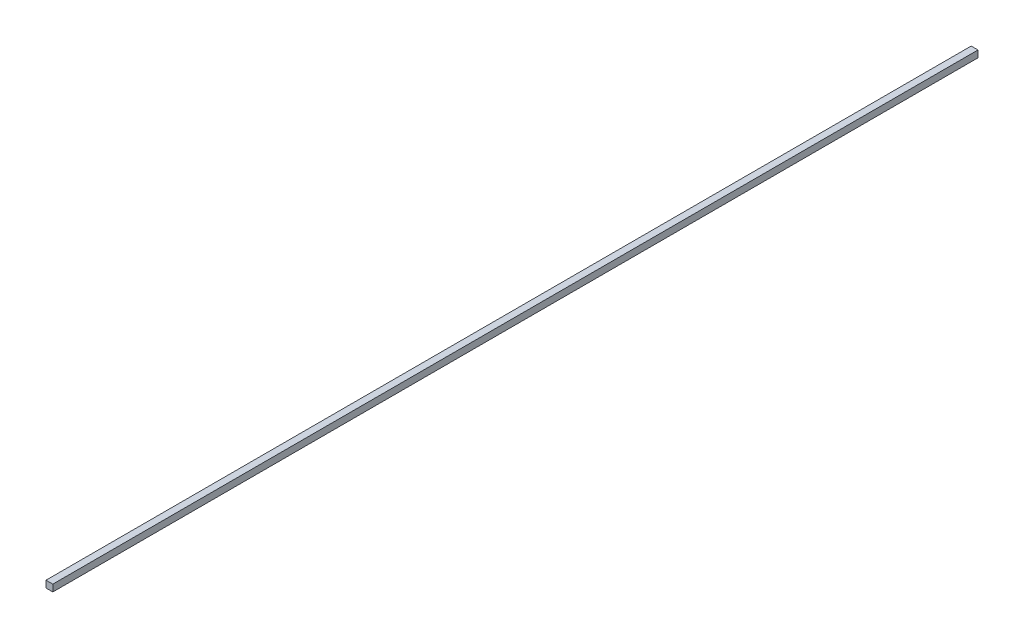
SolidWorks part; units mm, degrees
ref_plane "Plano frontal" through (0, 0, 0) normal (0, 0, 1) x (1, 0, 0)
ref_plane "Plano superior" through (0, 0, 0) normal (0, 1, 0) x (1, 0, 0)
ref_plane "Plano direito" through (0, 0, 0) normal (1, 0, 0) x (0, 0, -1)
sketch "Esboço1" plane through (0, 0, 0) normal (0, 0, 1) x (1, 0, 0)
  line L1 (0, 0) -> (35, 0)
  line L2 (0, 0) -> (0, 35)
  line L3 (0, 35) -> (35, 35)
  line L4 (35, 0) -> (35, 35)
  dimension "D1" = 35
  dimension "D2" = 35
extrude "Ressalto-extrusão1" add sketch "Esboço1" along normal blind 4750
